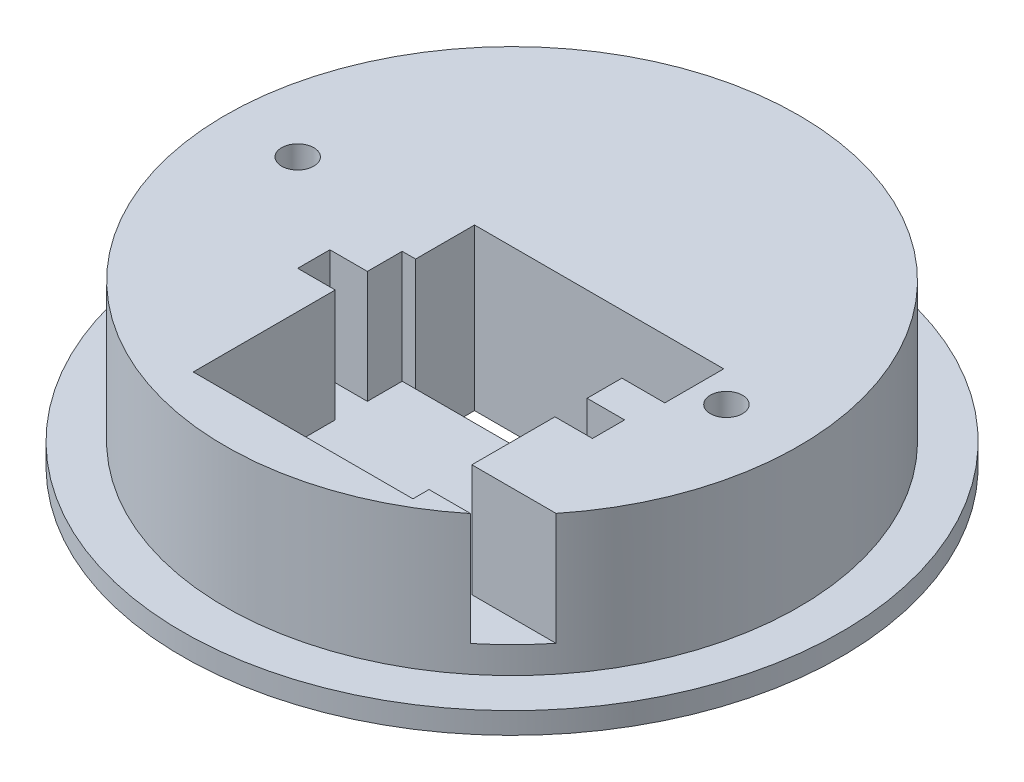
SolidWorks part; units mm, degrees
ref_plane "Plan de face" through (0, 0, 0) normal (0, 0, 1) x (1, 0, 0)
ref_plane "Plan de dessus" through (0, 0, 0) normal (0, 1, 0) x (1, 0, 0)
ref_plane "Plan de droite" through (0, 0, 0) normal (1, 0, 0) x (0, 0, -1)
sketch "Esquisse1" plane through (0, 0, 0) normal (0, 1, 0) x (1, 0, 0)
  line L0 (-12.5, 5.5) -> (12.5, -5.5) construction
  line L1 (-12.5, 5.5) -> (12.5, 5.5)
  line L2 (-12.5, 5.5) -> (-12.5, -5.5)
  line L3 (-12.5, -5.5) -> (12.5, -5.5)
  line L4 (12.5, 5.5) -> (12.5, -5.5)
  line L5 (0, 5.5) -> (0, -5.5) construction
  line L6 (-40, 0) -> (0, 0) construction
  arc A0 (68.1069, 104.8163) -> (39.4847, 118.6) centre (0, 0) ccw
  circle A4 centre (0, 125) radius 40 construction
  arc A5 (-39.4847, 118.6) -> (39.4847, 118.6) centre (0, 125) ccw
  arc A6 (68.1069, 104.8163) -> (117.3435, 43.0755) centre (97.7289, 77.9362) ccw
  arc A7 (124.4126, 12.1037) -> (106.8403, -64.8857) centre (121.866, -27.8151) ccw
  arc A8 (87.0331, -89.7231) -> (15.8841, -123.9867) centre (54.2355, -112.6211) ccw
  arc A9 (-15.8841, -123.9867) -> (-87.0331, -89.7231) centre (-54.2355, -112.6211) ccw
  arc A10 (-106.8403, -64.8857) -> (-124.4126, 12.1037) centre (-121.866, -27.8151) ccw
  arc A11 (-117.3435, 43.0755) -> (-68.1069, 104.8163) centre (-97.7289, 77.9362) ccw
  arc A12 (124.4126, 12.1037) -> (117.3435, 43.0755) centre (0, 0) ccw
  arc A13 (87.0331, -89.7231) -> (106.8403, -64.8857) centre (0, 0) ccw
  arc A14 (-15.8841, -123.9867) -> (15.8841, -123.9867) centre (0, 0) ccw
  arc A15 (-106.8403, -64.8857) -> (-87.0331, -89.7231) centre (0, 0) ccw
  arc A16 (-117.3435, 43.0755) -> (-124.4126, 12.1037) centre (0, 0) ccw
  arc A17 (-39.4847, 118.6) -> (-68.1069, 104.8163) centre (0, 0) ccw
  circle A18 centre (-40, 0) radius 3
  circle A19 centre (40, 0) radius 3
  point P6 (0, 0)
  point P8 (0, 0)
  point P36 (0, 0)
  dimension "D1" = 250
  dimension "D4" = 6
  dimension "D5" = 40
  dimension "D7" = 80
  dimension "D3" = 25
  dimension "D2" = 11
  dimension "D8" = 7
extrude "Boss.-Extru.1" add sketch "Esquisse1" along normal blind 30
sketch "Esquisse2" plane through (0, 30, 0) normal (0, 1, 0) x (1, 0, 0)
  circle A0 centre (0, 0) radius 53.5
  circle A1 centre (0, 0) radius 125
  dimension "D1" = 107
extrude "Enlèv. mat.-Extru.1" cut sketch "Esquisse2" against normal through all
sketch "Esquisse8" plane through (0, 0, 0) normal (0, -1, 0) x (1, 0, 0)
  circle A0 centre (0, 0) radius 53.5
  circle A1 centre (0, 0) radius 61.5
  dimension "D1" = 123
  dimension "D2" = 107
extrude "Boss.-Extru.2" add sketch "Esquisse8" against normal blind 4
sketch "Esquisse5" plane through (0, 0, 5.5) normal (0, 0, -1) x (-1, 0, 0)
  line L0 (53.5, 30) -> (-53.5, 30) construction
  line L1 (0, 0) -> (0, 30) construction
  line L2 (-12.5, 30) -> (12.5, 30) construction
  circle A0 centre (-16, 19) radius 18
  dimension "D1" = 36
  dimension "D2" = 11
  dimension "D3" = 16
extrude "Enlèv. mat.-Extru.2" cut sketch "Esquisse5" along normal up to surface (11 mm away) up to face at (0, 15, -5.5)
sketch "Esquisse6" plane through (0, 30, 0) normal (0, 1, 0) x (1, 0, 0)
  line L0 (30.2478, -5.5) -> (-12.5, -5.5) construction
  line L1 (-15, -44.5) -> (26, -44.5)
  line L2 (-15, -44.5) -> (-15, -5.5)
  line L3 (-15, -5.5) -> (26, -5.5)
  line L4 (26, -44.5) -> (26, -5.5)
  line L5 (-15, -12) -> (-22, -12)
  line L6 (-15, -12) -> (-15, -18)
  line L7 (-15, -18) -> (-22, -18)
  line L8 (-22, -12) -> (-22, -18)
  line L9 (26, -18) -> (33, -18)
  line L10 (26, -18) -> (26, -12)
  line L11 (26, -12) -> (33, -12)
  line L12 (33, -18) -> (33, -12)
  line L13 (16, -5.5) -> (16, -16.5506) construction
  line L15 (16, 5.5) -> (16, -5.5) construction
  line L16 (26, -33.5) -> (43, -33.5)
  line L17 (26, -33.5) -> (26, -41.5)
  line L18 (26, -41.5) -> (43, -41.5)
  line L19 (43, -33.5) -> (43, -41.5)
  dimension "D1" = 39
  dimension "D2" = 41
  dimension "D3" = 26.5
  dimension "D4" = 6
  dimension "D5" = 7
  dimension "D6" = 10
  dimension "D7" = 8
  dimension "D8" = 3
  dimension "D9" = 17
extrude "Enlèv. mat.-Extru.3" cut sketch "Esquisse6" against normal blind 21
sketch "Esquisse7" plane through (0, 30, 0) normal (0, 1, 0) x (1, 0, 0)
  line L1 (34, -5.5) -> (-2, -5.5)
  line L2 (34, -5.5) -> (34, 5.5)
  line L3 (34, 5.5) -> (-2, 5.5)
  line L4 (-2, -5.5) -> (-2, 5.5)
  line L5 (-12.5, 5.5) -> (30.2478, 5.5) construction
  line L6 (16, 5.5) -> (16, -5.5) construction
  dimension "D1" = 36
  dimension "D2" = 16
  dimension "D3" = 11
extrude "Enlèv. mat.-Extru.4" cut sketch "Esquisse7" against normal blind 11
